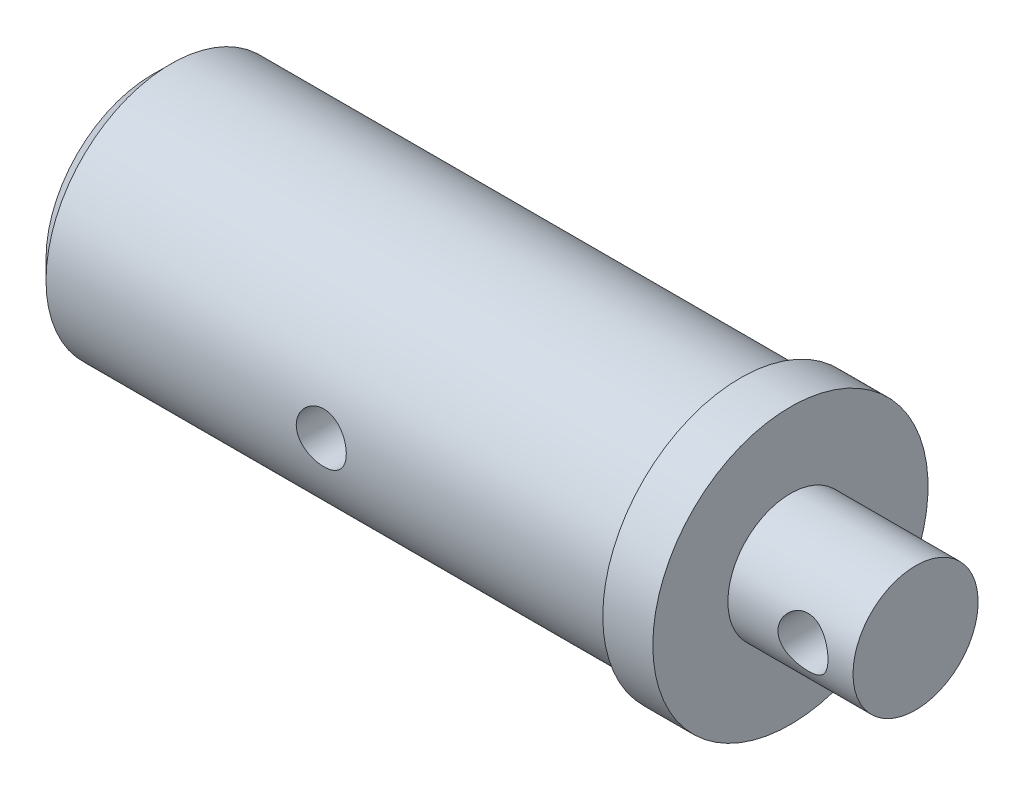
SolidWorks part; units mm, degrees
material "6061-T4 (SS)"
ref_plane "Płaszczyzna XY" through (0, 0, 0) normal (0, 0, 1) x (1, 0, 0)
ref_plane "Płaszczyzna XZ" through (0, 0, 0) normal (0, 1, 0) x (1, 0, 0)
ref_plane "Płaszczyzna YZ" through (0, 0, 0) normal (1, 0, 0) x (0, 0, -1)
sketch "Szkic1" plane through (0, 0, 0) normal (0, 1, 0) x (1, 0, 0)
  line L0 (-22, 0) -> (39, 0)
  line L1 (39, 0) -> (39, 5)
  line L2 (39, 5) -> (29, 5)
  line L3 (29, 5) -> (29, 11)
  line L4 (29, 11) -> (25, 11)
  line L5 (25, 11) -> (25, 10)
  line L6 (25, 10) -> (-22, 10)
  line L7 (-22, 10) -> (-22, 0)
  dimension "D1" = 61
  dimension "D2" = 10
  dimension "D3" = 4
  dimension "D4" = 5
  dimension "D5" = 10
  dimension "D6" = 11
revolve "Obrót1" add sketch "Szkic1" angle 360 about L0
sketch "Szkic3" plane through (-22, 0, 0) normal (-1, 0, 0) x (0, 0, 1)
  circle A0 centre (0, 0) radius 6
  dimension "D1" = 12
extrude "Wytnij-wyciągnięcie1" cut sketch "Szkic3" against normal blind 30 contours A0
chamfer "Sfazowanie1" distance 1.5 angle 45 1 edges at (-22, 0, 10)
ref_plane "Płaszczyzna1" through (0, 0, 0) normal (0, 0, 1) x (1, 0, 0)
sketch "Szkic6" plane through (0, 0, 0) normal (0, 0, 1) x (1, 0, 0)
  line L0 (25, 0) -> (-22, 0) construction
  line L1 (25, 11) -> (25, -11) construction
  line L2 (-22, 6) -> (-22, -6) construction
  line L3 (29, 0) -> (35, 0) construction
  line L4 (29, -5) -> (29, 5) construction
  circle A0 centre (35, 0) radius 2
  circle A1 centre (1.5, 0) radius 2
  point P11 (1.5, 0)
  dimension "D1" = 6
extrude "Wytnij-wyciągnięcie4" cut sketch "Szkic6" against normal mid plane 30
